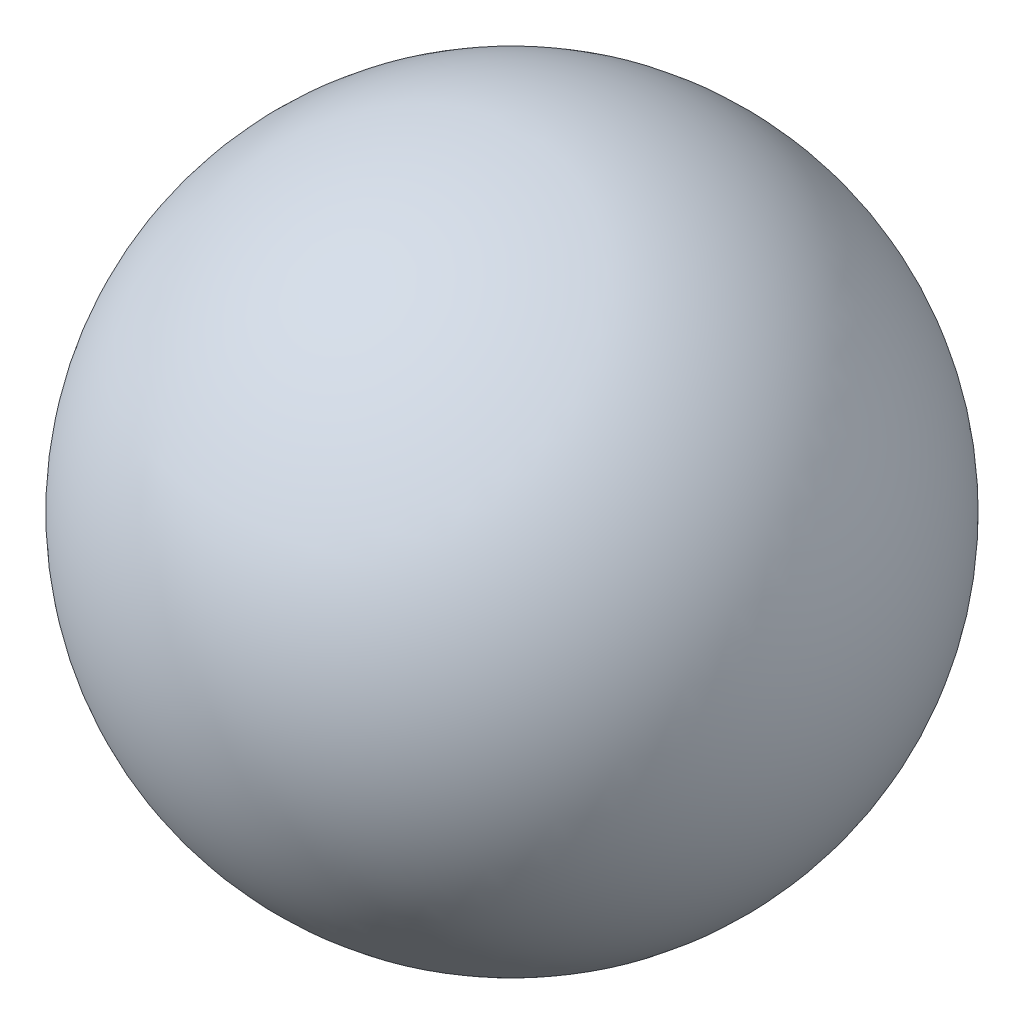
SolidWorks part; units mm, degrees
ref_plane "Front Plane" through (0, 0, 0) normal (0, 0, 1) x (1, 0, 0)
ref_plane "Top Plane" through (0, 0, 0) normal (0, 1, 0) x (1, 0, 0)
ref_plane "Right Plane" through (0, 0, 0) normal (1, 0, 0) x (0, 0, -1)
sketch "Sketch1" plane through (0, 0, 0) normal (0, 0, 1) x (1, 0, 0)
  line L0 (0, -10) -> (0, 10) construction
  line L1 (0, -10) -> (0, 10)
  arc A0 (0, -10) -> (0, 10) centre (0, 0) ccw
  dimension "D1" = 10
revolve "Revolve2" add sketch "Sketch1" angle 360 about L0
equation "\"radius\"=10"
